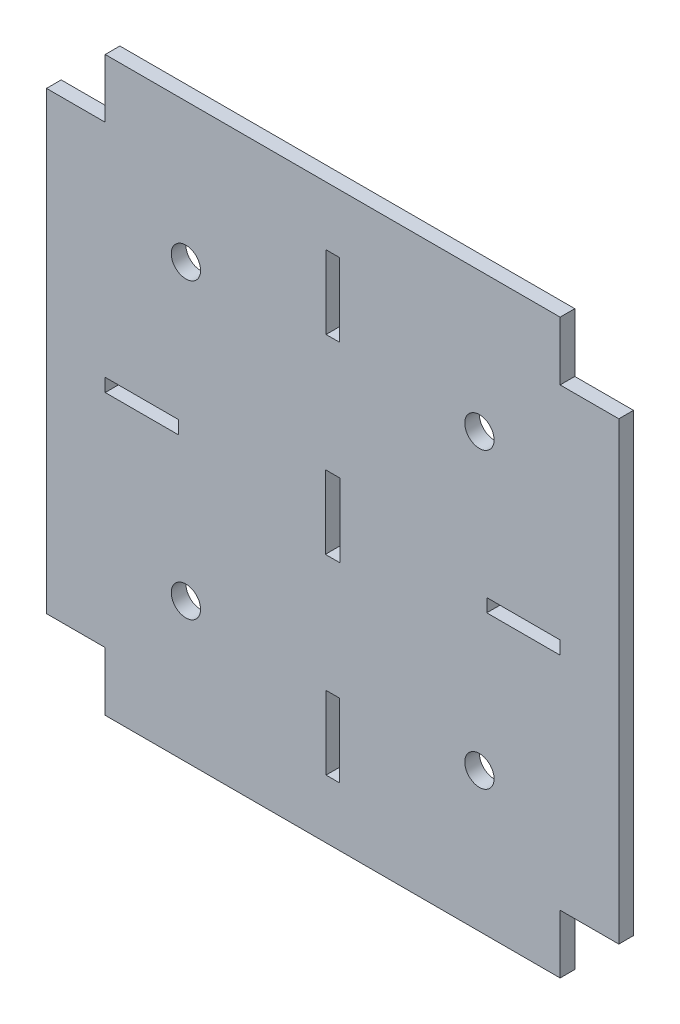
SolidWorks part; units mm, degrees
ref_plane "前基準面" through (0, 0, 0) normal (0, 0, 1) x (1, 0, 0)
ref_plane "上基準面" through (0, 0, 0) normal (0, 1, 0) x (1, 0, 0)
ref_plane "右基準面" through (0, 0, 0) normal (1, 0, 0) x (0, 0, -1)
sketch "草圖1" plane through (0, 0, 0) normal (0, 0, 1) x (1, 0, 0)
  line L0 (0, 0) -> (0, 31.2574) construction
  line L1 (-31, 39) -> (31, 39)
  line L2 (-39, 31) -> (-39, -31)
  line L3 (-31, -39) -> (31, -39)
  line L4 (39, 31) -> (39, -31)
  line L5 (-0.9, -21) -> (0.9, -21)
  line L6 (-0.9, 31) -> (0.9, 31)
  line L7 (-39, 31) -> (-31, 31)
  line L8 (-31, 39) -> (-31, 31)
  line L9 (-0.9, 31) -> (-0.9, 21)
  line L10 (-0.9, 21) -> (0.9, 21)
  line L11 (39, 31) -> (31, 31)
  line L12 (31, 39) -> (31, 31)
  line L13 (0.9, 31) -> (0.9, 21)
  line L14 (-31, 0.9) -> (-21, 0.9)
  line L15 (-39, -31) -> (-31, -31)
  line L16 (-31, -39) -> (-31, -31)
  line L17 (-31, 0.9) -> (-31, -0.9)
  line L18 (-31, -0.9) -> (-21, -0.9)
  line L19 (39, -31) -> (31, -31)
  line L20 (31, -39) -> (31, -31)
  line L21 (0, 0) -> (-54.2411, 0) construction
  line L22 (-21, 0.9) -> (-21, -0.9)
  line L23 (0.9, -31) -> (0.9, -21)
  line L24 (-0.9, -31) -> (0.9, -31)
  line L25 (-0.9, -31) -> (-0.9, -21)
  line L26 (31, 0.9) -> (31, -0.9)
  line L27 (21, 0.9) -> (21, -0.9)
  line L28 (31, 0.9) -> (21, 0.9)
  line L29 (31, -0.9) -> (21, -0.9)
  line L31 (-1, 5) -> (1, 5)
  line L32 (-1, 5) -> (-1, -5)
  line L33 (-1, -5) -> (1, -5)
  line L34 (1, 5) -> (1, -5)
  circle A0 centre (-20, 20) radius 2
  circle A1 centre (20, 20) radius 2
  circle A2 centre (20, -20) radius 2
  circle A3 centre (-20, -20) radius 2
  point P4 (39, 0)
  point P6 (0, 39)
  dimension "D11" = 4
  dimension "D1" = 78
  dimension "D2" = 62
  dimension "D3" = 62
  dimension "D4" = 78
  dimension "D5" = 1.8
  dimension "D6" = 10
  dimension "D7" = 1.8
  dimension "D8" = 10
  dimension "D9" = 20
  dimension "D10" = 20
  dimension "D14" = 40
  dimension "D15" = 40
  dimension "D16" = 10
  dimension "D17" = 2
  dimension "D12" = 2
  dimension "D13" = 2
extrude "填料-伸長1" add sketch "草圖1" along normal blind 2
